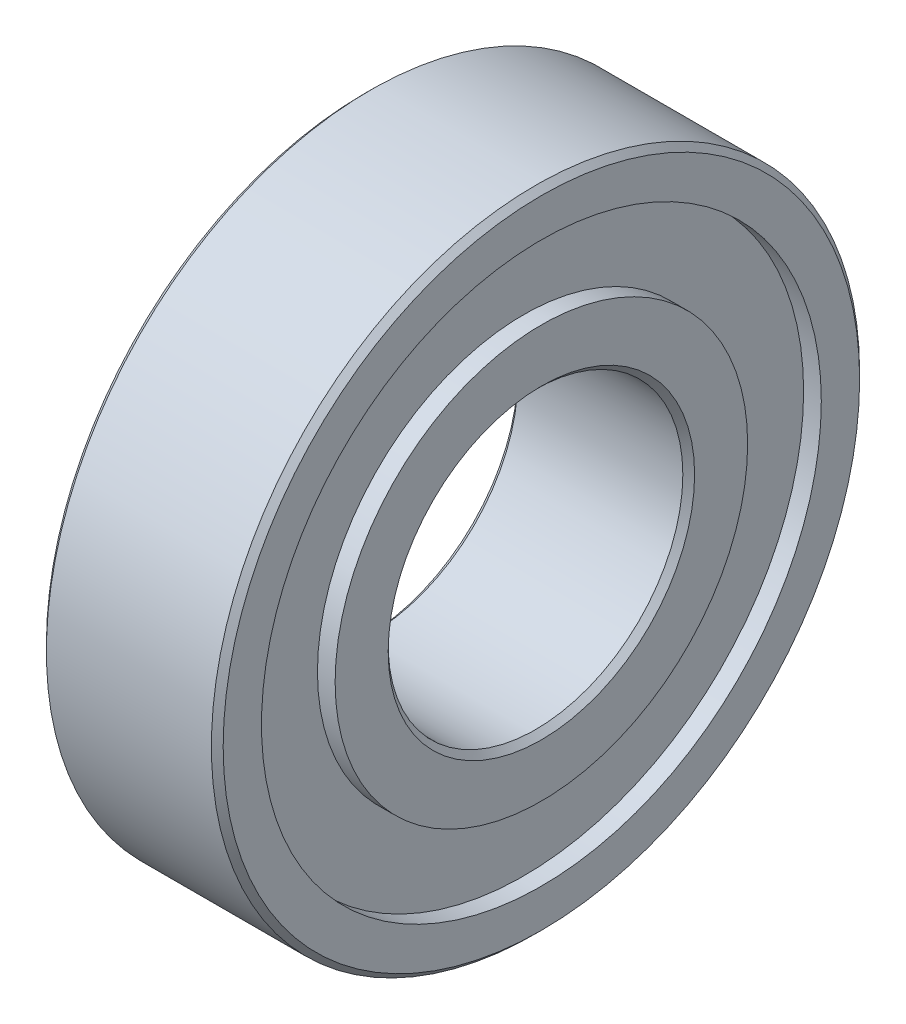
SolidWorks part; units mm, degrees
ref_plane "前视基准面" through (0, 0, 0) normal (0, 0, 1) x (1, 0, 0)
ref_plane "上视基准面" through (0, 0, 0) normal (0, 1, 0) x (1, 0, 0)
ref_plane "右视基准面" through (0, 0, 0) normal (1, 0, 0) x (0, 0, -1)
sketch "草图1" plane through (0, 0, 0) normal (1, 0, 0) x (0, 0, -1)
  circle A0 centre (0, 0) radius 5
  circle A1 centre (0, 0) radius 11
  dimension "D1" = 10
  dimension "D2" = 22
extrude "凸台-拉伸1" add sketch "草图1" along normal blind 6
sketch "草图2" plane through (6, 0, 0) normal (1, 0, 0) x (0, 0, -1)
  circle A0 centre (-0.0004, 0) radius 7
  circle A1 centre (-0.0004, 0) radius 9.4996
  circle A2 centre (0, 0) radius 11 construction
  dimension "D1" = 1.5
  dimension "D2" = 14
extrude "切除-拉伸1" cut sketch "草图2" against normal blind 0.6
sketch "草图3" plane through (0, 0, 0) normal (-1, 0, 0) x (0, 0, 1)
  circle A0 centre (0.4509, 0) radius 7
  circle A1 centre (0.4509, 0) radius 9.9509
  circle A2 centre (0, 0) radius 11 construction
  dimension "D1" = 14
  dimension "D2" = 1.5
extrude "切除-拉伸2" cut sketch "草图3" against normal blind 0.6
chamfer "倒角1" distance 0.2 angle 45 4 edges at (6, 0, -11) (0, 0, -11) (6, 0, -5) (0, 0, -5)
